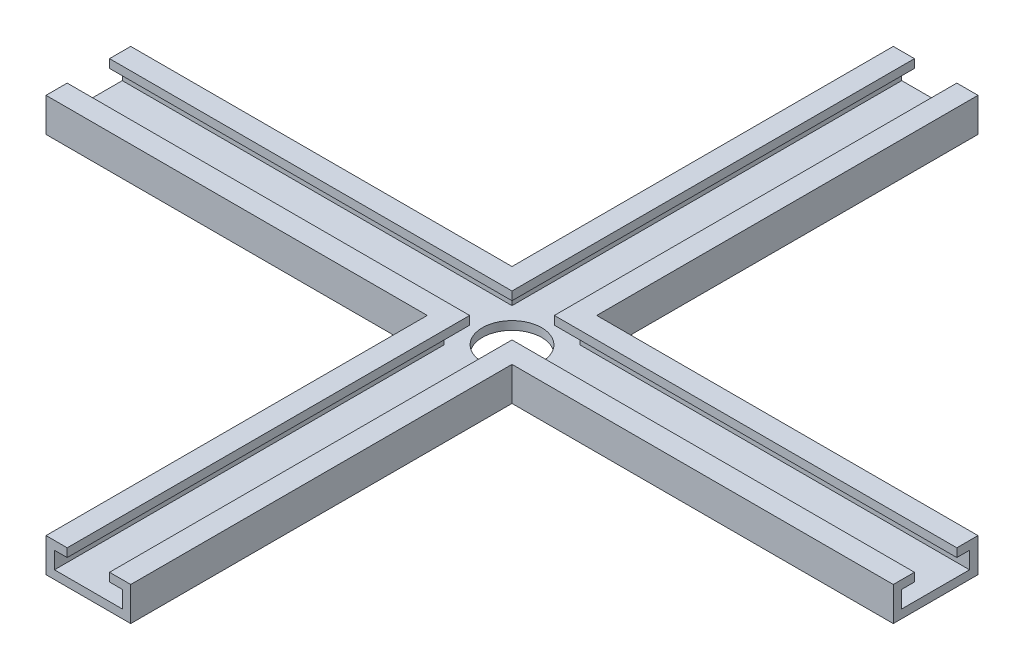
SolidWorks part; units mm, degrees
ref_plane "前视基准面" through (0, 0, 0) normal (0, 0, 1) x (1, 0, 0)
ref_plane "上视基准面" through (0, 0, 0) normal (0, 1, 0) x (1, 0, 0)
ref_plane "右视基准面" through (0, 0, 0) normal (1, 0, 0) x (0, 0, -1)
sketch "草图1" plane through (0, 0, 0) normal (0, 0, 1) x (1, 0, 0)
  line L0 (0, 0) -> (10, 0)
  line L1 (10, 0) -> (10, 8)
  line L2 (10, 8) -> (5, 8)
  line L3 (0, 2) -> (8, 2)
  line L4 (8, 2) -> (8, 6)
  line L5 (8, 6) -> (5, 6)
  line L6 (5, 8) -> (5, 6)
  line L7 (0, -10.0227) -> (0, 24.2579) construction
  line L8 (0, 2) -> (-8, 2)
  line L9 (-8, 6) -> (-5, 6)
  line L10 (-5, 8) -> (-5, 6)
  line L11 (-8, 2) -> (-8, 6)
  line L12 (-10, 8) -> (-5, 8)
  line L13 (-10, 0) -> (-10, 8)
  line L14 (0, 0) -> (-10, 0)
  dimension "D1" = 10
  dimension "D2" = 8
  dimension "D3" = 5
  dimension "D4" = 2
extrude "凸台-拉伸1" add sketch "草图1" along normal blind 200
sketch "草图2" plane through (0, 0, 0) normal (1, 0, 0) x (0, 0, -1)
  line L0 (-100, 0) -> (-90, 0)
  line L1 (-200, 0) -> (0, 0) construction
  line L2 (-90, 0) -> (-90, 8)
  line L3 (-200, 8) -> (0, 8) construction
  line L4 (-90, 8) -> (-95, 8)
  line L5 (-100, 2) -> (-92, 2)
  line L6 (-92, 2) -> (-92, 6)
  line L7 (-92, 6) -> (-95, 6)
  line L8 (-95, 6) -> (-95, 8)
  line L9 (-100, 0) -> (-100, 10.9617) construction
  line L10 (-100, 0) -> (-110, 0)
  line L11 (-110, 0) -> (-110, 8)
  line L12 (-110, 8) -> (-105, 8)
  line L13 (-105, 6) -> (-105, 8)
  line L14 (-108, 6) -> (-105, 6)
  line L15 (-108, 2) -> (-108, 6)
  line L16 (-100, 2) -> (-108, 2)
  dimension "D1" = 10
  dimension "D2" = 8
  dimension "D3" = 5
  dimension "D4" = 2
extrude "凸台-拉伸2" add sketch "草图2" along normal mid plane 200
sketch "草图3" plane through (100, 0, 0) normal (1, 0, 0) x (0, 0, -1)
  line L0 (-95, 8) -> (-95, 6) construction
  line L1 (-108, 6) -> (-105, 6)
  line L2 (-108, 6) -> (-108, 2)
  line L3 (-108, 2) -> (-92, 2)
  line L4 (-92, 6) -> (-92, 2)
  line L5 (-105, 8) -> (-95, 8)
  line L6 (-105, 8) -> (-105, 6)
  line L8 (-95, 8) -> (-95, 6)
  line L9 (-95, 6) -> (-92, 6)
extrude "切除-拉伸1" cut sketch "草图3" against normal blind 200
sketch "草图4" plane through (0, 0, 200) normal (0, 0, 1) x (1, 0, 0)
  line L0 (5, 6) -> (8, 6)
  line L1 (-8, 6) -> (-5, 6)
  line L2 (-8, 6) -> (-8, 2)
  line L3 (-8, 2) -> (8, 2)
  line L4 (8, 6) -> (8, 2)
  line L5 (-5, 8) -> (5, 8)
  line L6 (-5, 8) -> (-5, 6)
  line L8 (5, 8) -> (5, 6)
extrude "切除-拉伸2" cut sketch "草图4" against normal blind 200
sketch "草图5" plane through (0, 0, 0) normal (0, -1, 0) x (1, 0, 0)
  line L0 (-10, 90) -> (10, 110)
  circle A0 centre (0, 100) radius 7
extrude "切除-拉伸3" cut sketch "草图5" against normal blind 15 contours L0 A0 | L0 A0
